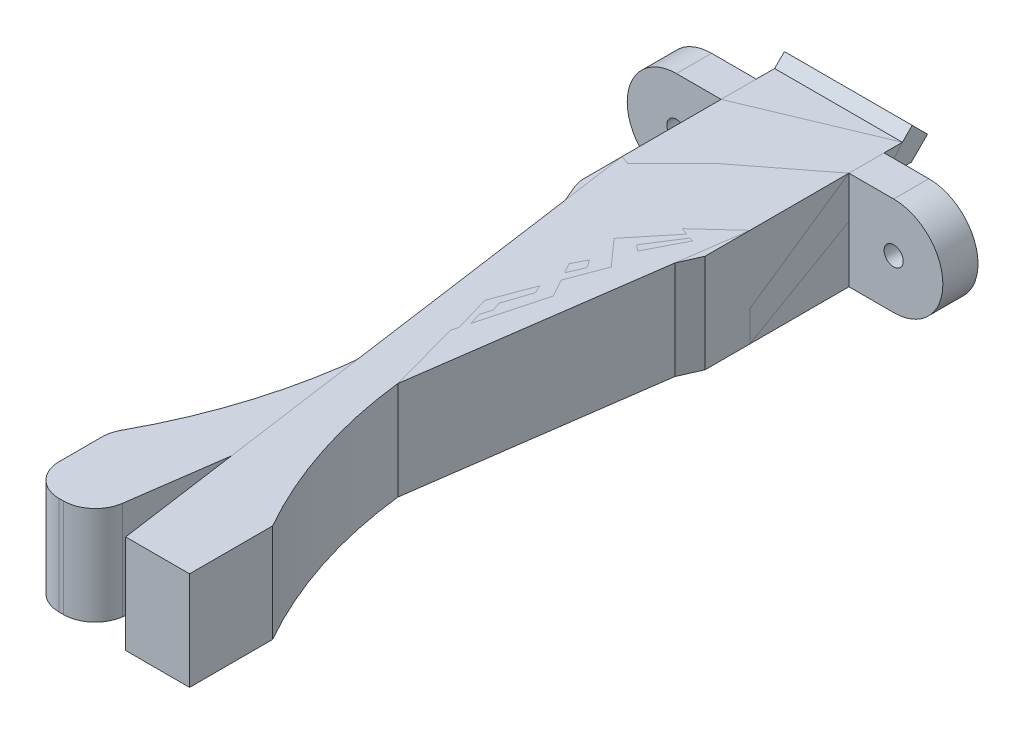
SolidWorks part; units mm, degrees
ref_plane "Front Plane" through (0, 0, 0) normal (0, 0, 1) x (1, 0, 0)
ref_plane "Top Plane" through (0, 0, 0) normal (0, 1, 0) x (1, 0, 0)
ref_plane "Right Plane" through (0, 0, 0) normal (1, 0, 0) x (0, 0, -1)
sketch "Sketch2" plane through (0, 0, 0) normal (0, 0, 1) x (1, 0, 0)
  line L0 (0, 5.9203) -> (0, 8.9503) construction
  line L1 (-5, -5.8182) -> (5, -5.8182)
  line L2 (-5, -5.8182) -> (-5, 8.9503)
  line L3 (-5, 8.9503) -> (5, 8.9503)
  line L4 (5, -5.8182) -> (5, 8.9503)
  line L7 (13.4766, 5.9203) -> (-18.5234, 5.9203) construction
  line L8 (0, -5.8182) -> (0, -2.7882) construction
  point P0 (0, 0)
  dimension "D1" = 10
extrude "Boss-Extrude1" add sketch "Sketch2" along normal blind 5
sketch "Sketch8" plane through (-5, 0, 0) normal (-1, 0, 0) x (0, 0, 1)
  line L6 (-0.15, 5.7703) -> (0, 5.7703)
  line L7 (0, 8.9503) -> (0, -5.8182) construction
  line L8 (0, 5.7703) -> (0, 4.0703)
  line L9 (0, 4.0703) -> (-0.15, 4.0703)
  line L11 (-0.15, -1.9297) -> (0, -1.9297)
  line L12 (-2.1379, 4.0703) -> (-0.15, 4.0703)
  line L13 (-0.15, 4.0703) -> (-0.15, 5.7703)
  line L14 (-0.15, 5.7703) -> (-1.4337, 5.7703)
  line L15 (-1.4337, 5.7703) -> (-2.2, 6.5366)
  line L16 (-2.2, 6.5366) -> (-3.4021, 5.3345)
  line L17 (-3.4021, 5.3345) -> (-2.1379, 4.0703)
  line L18 (-2.1379, 4.0703) -> (-0.15, 4.0703)
  line L20 (-0.15, 5.7703) -> (-1.4337, 5.7703)
  line L21 (-1.4337, 5.7703) -> (-2.2, 6.5366)
  line L22 (-2.2, 6.5366) -> (-3.4021, 5.3345)
  line L23 (-3.4021, 5.3345) -> (-2.1379, 4.0703)
  line L24 (-2.1379, -1.9297) -> (-0.15, -1.9297)
  line L25 (-0.15, -1.9297) -> (-0.15, -0.2297)
  line L26 (-0.15, -0.2297) -> (-1.4337, -0.2297)
  line L27 (-1.4337, -0.2297) -> (-2.2, 0.5366)
  line L28 (-2.2, 0.5366) -> (-3.4021, -0.6655)
  line L29 (-3.4021, -0.6655) -> (-2.1379, -1.9297)
  line L30 (-2.1379, -1.9297) -> (-0.15, -1.9297)
  line L32 (-0.15, -0.2297) -> (-1.4337, -0.2297)
  line L33 (-1.4337, -0.2297) -> (-2.2, 0.5366)
  line L34 (-2.2, 0.5366) -> (-3.4021, -0.6655)
  line L35 (-3.4021, -0.6655) -> (-2.1379, -1.9297)
  line L37 (-0.15, -0.2297) -> (0, -0.2297)
  line L38 (0, -1.9297) -> (0, -0.2297)
  dimension "D1" = 0.15
  dimension "D2" = 0.15
extrude "Boss-Extrude4" add sketch "Sketch8" against normal up to surface (10 mm away) up to face at (5, 1.566, 2.5)
sketch "Sketch9" plane through (0, 0, 0) normal (0, 0, -1) x (-1, 0, 0)
  line L4 (-5, 8.9503) -> (-5, 5.7703)
  line L5 (-5, 5.7703) -> (5, 5.7703)
  line L6 (5, 5.7703) -> (5, 8.9503)
  line L7 (5, 8.9503) -> (-5, 8.9503)
  line L8 (-5, 8.9503) -> (-5, 5.7703)
  line L10 (5, 5.7703) -> (5, 8.9503)
  line L11 (5, 8.9503) -> (-5, 8.9503)
  line L16 (5, -1.9297) -> (-5, -1.9297)
  line L17 (-5, -1.9297) -> (-5, -5.8182)
  line L18 (-5, -5.8182) -> (5, -5.8182)
  line L19 (5, -5.8182) -> (5, -1.9297)
  line L21 (-5, -1.9297) -> (-5, -5.8182)
  line L22 (-5, -5.8182) -> (5, -5.8182)
  line L23 (5, -5.8182) -> (5, -1.9297)
  line L26 (-5, 5.7703) -> (5, 5.7703)
  line L27 (5, -1.9297) -> (-5, -1.9297)
  dimension "D1" = 0
  dimension "D2" = 0
extrude "Cut-Extrude3" cut sketch "Sketch9" against normal blind 5
sketch "Sketch10" plane through (0, 5.7703, 0) normal (0, 1, 0) x (1, 0, 0)
  line L0 (-5, -5) -> (-5, -10.5)
  line L1 (-5, -10.5) -> (1.3524, -55.7)
  line L2 (1.3524, -55.7) -> (6.3524, -55.7)
  line L3 (-5, -5) -> (5, -5)
  line L4 (-120.9789, 453.7107) -> (412.3545, 453.7107) construction
  line L5 (6.3524, -55.7) -> (6.3524, -49.2)
  line L6 (5, -5) -> (5, -14)
  arc A1 (5, -14) -> (6.3524, -49.2) centre (39.6089, -30.2962) ccw
  dimension "D1" = 172
  dimension "D2" = 45.2
  dimension "D3" = 5
  dimension "D4" = 6.5
  dimension "D5" = 5.5
  dimension "D6" = 9
extrude "Boss-Extrude5" add sketch "Sketch10" against normal up to surface (7.7 mm away) up to face at (0, -1.9297, 1.4311)
ref_plane "Plane1" through (0, 0, 2.75) normal (0, 0, 1) x (1, 0, 0)
sketch "Sketch12" plane through (0, 0, 0) normal (0, 0, 1) x (1, 0, 0)
  line L0 (5, 5.7703) -> (8.5, 5.7703)
  line L1 (8.5, -1.9297) -> (5, -1.9297)
  line L2 (5, -1.9297) -> (5, 5.7703)
  line L3 (1.3524, 5.7703) -> (6.3524, 5.7703) construction
  line L4 (1.3524, -1.9297) -> (6.3524, -1.9297) construction
  line L5 (5, 5.3345) -> (5, 6.5366) construction
  line L6 (6.3524, 5.7703) -> (1.3552, 5.7703) construction
  arc A0 (8.5, 5.7703) -> (8.5, -1.9297) centre (8.5, 1.9203) cw
  circle A1 centre (8.5, 1.9203) radius 0.75
  dimension "D1" = 1.5
  dimension "D2" = 3.5
extrude "Boss-Extrude7" add sketch "Sketch12" along normal up to surface (2.75 mm away) up to plane "Plane1"
mirror "Mirror1" about plane through (0, 0, 0) normal (1, 0, 0) of bodies 112
fillet "Fillet1" radius 2.5 4 edges at (-6.3524, 1.9203, 49.2) (-5, 1.9203, 14) (-1.3524, 1.9203, 55.7) (-6.3524, 1.9203, 55.7)
